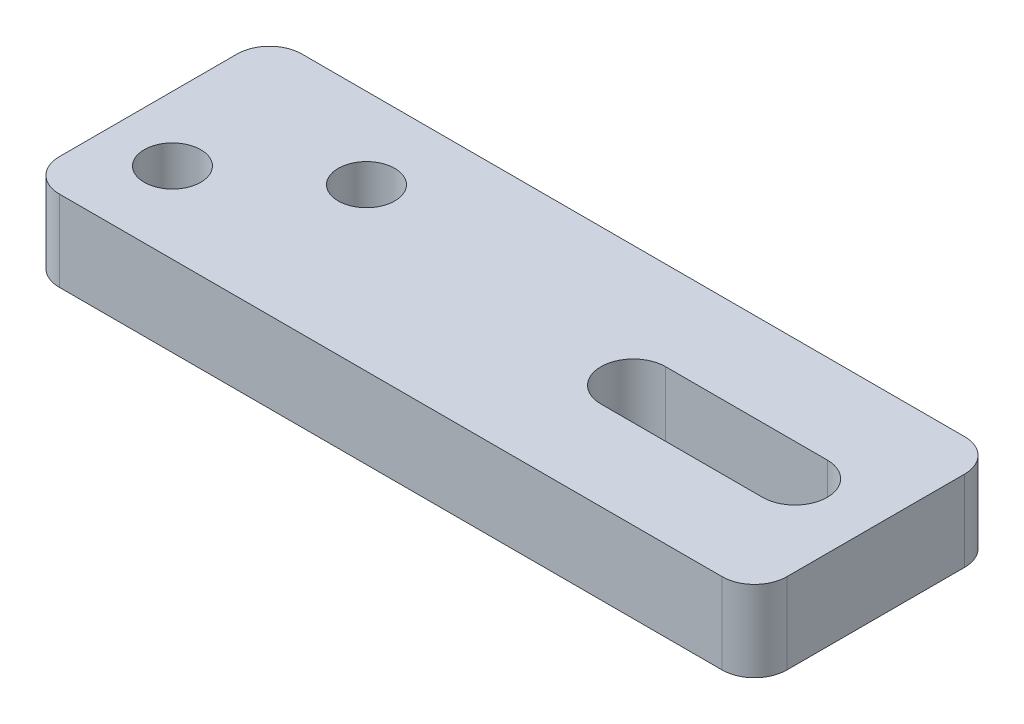
SolidWorks part; units mm, degrees
material "Thornel Mat VMA"
ref_plane "前视基准面" through (0, 0, 0) normal (0, 0, 1) x (1, 0, 0)
ref_plane "上视基准面" through (0, 0, 0) normal (0, 1, 0) x (1, 0, 0)
ref_plane "右视基准面" through (0, 0, 0) normal (1, 0, 0) x (0, 0, -1)
sketch "草图1" plane through (0, 0, 0) normal (0, 1, 0) x (1, 0, 0)
  line L0 (0, 5.5) -> (0, -5.5)
  line L1 (2, -7.5) -> (43, -7.5)
  line L2 (45, -5.5) -> (45, 5.5)
  line L3 (43, 7.5) -> (2, 7.5)
  line L4 (30.0281, -2) -> (40, -2)
  line L5 (30, 1.9998) -> (40, 2)
  circle A0 centre (4, -2.5) radius 1.75
  circle A1 centre (11, 2.5) radius 1.75
  arc A3 (30, 1.9998) -> (30.0281, -2) centre (30, -0.0002) ccw
  arc A4 (0, -5.5) -> (2, -7.5) centre (2, -5.5) ccw
  arc A5 (0, 5.5) -> (2, 7.5) centre (2, 5.5) cw
  arc A6 (45, 5.5) -> (43, 7.5) centre (43, 5.5) ccw
  arc A7 (43, -7.5) -> (45, -5.5) centre (43, -5.5) ccw
  arc A8 (40, -2) -> (39.9999, 2) centre (40, 0) ccw
  point P15 (0, -7.5)
  point P22 (0, 7.5)
  dimension "D3" = 3.5
  dimension "D4" = 3.5
  dimension "D9" = 40
  dimension "D12" = 5
  dimension "D13" = 4
  dimension "D14" = 2
  dimension "D15" = 2
  dimension "D10" = 4
  dimension "D1" = 15
  dimension "D2" = 4
  dimension "D5" = 7
  dimension "D6" = 5
  dimension "D7" = 5
  dimension "D8" = 10
  dimension "D11" = 7.5002
extrude "凸台-拉伸1" add sketch "草图1" along normal blind 5
